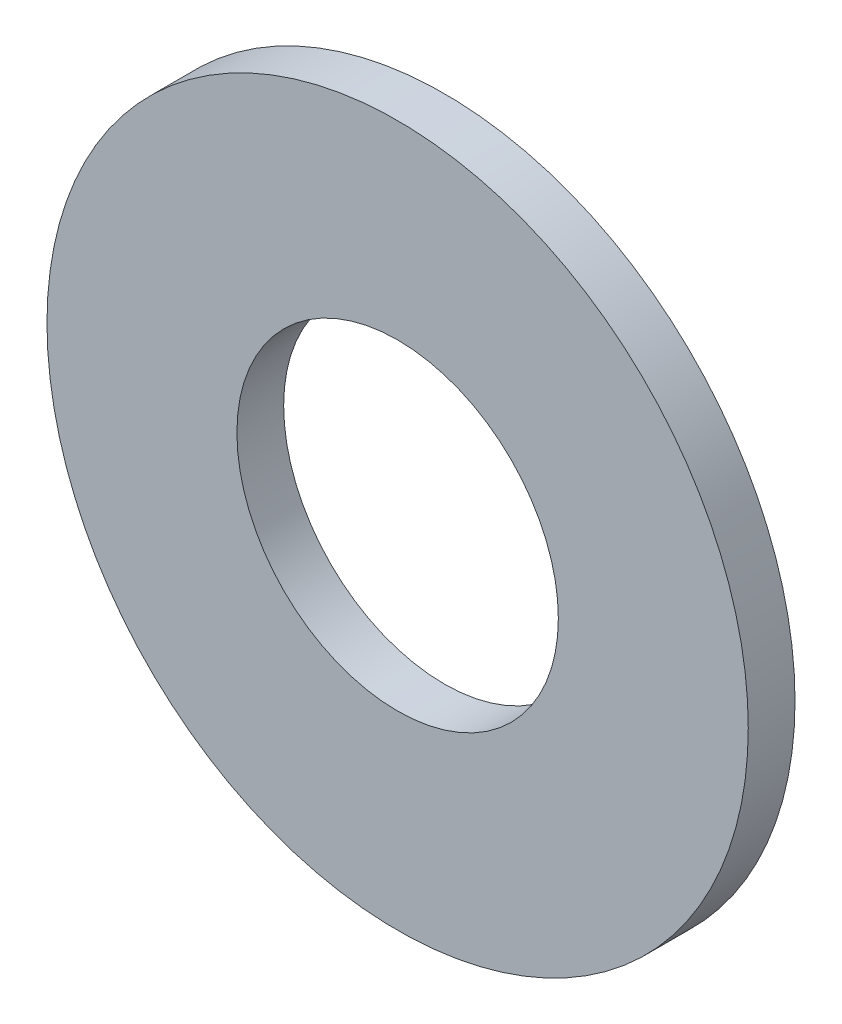
SolidWorks part; units mm, degrees
ref_plane "Front Plane" through (0, 0, 0) normal (0, 0, 1) x (1, 0, 0)
ref_plane "Top Plane" through (0, 0, 0) normal (0, 1, 0) x (1, 0, 0)
ref_plane "Right Plane" through (0, 0, 0) normal (1, 0, 0) x (0, 0, -1)
sketch "Sketch1" plane through (0, 0, 0) normal (0, 0, 1) x (1, 0, 0)
  circle A0 centre (0, 0) radius 6 construction
  circle A1 centre (0, 0) radius 2.75 construction
  point P5 (-2.75, 0)
  point P6 (2.75, 0)
  point P7 (6, 0)
  point P8 (-6, 0)
  point P9 (0, 0)
  point P10 (0, -2.75)
  dimension "OD" = 12
  dimension "ID" = 5.5
sketch "Sketch2" plane through (0, 0, 0) normal (1, 0, 0) x (0, 0, -1)
  line L0 (0, 6) -> (0, -6) construction
  line L1 (0, 6) -> (0, -6) construction
  line L2 (-0.4, 6) -> (0.4, 6) construction
  line L3 (-0.4, 0) -> (0.4, 0) construction
  line L4 (-0.4, -6) -> (0.4, -6) construction
  line L5 (0.4, -6) -> (0.4, 6) construction
  line L6 (-0.4, -6) -> (-0.4, 6) construction
  point P5 (0, 6)
  point P8 (0, 0)
  point P11 (0, -6)
  point P12 (0.4, 6)
  point P13 (0.4, 0)
  point P14 (0.4, -6)
  point P15 (-0.4, -6)
  point P16 (-0.4, 0)
  point P17 (-0.4, 6)
  dimension "Thickness Range" = 0.8
sketch "Sketch3" plane through (0, 0, 0) normal (0, 0, 1) x (1, 0, 0)
  circle A0 centre (0, 0) radius 6 construction
  circle A1 centre (0, 0) radius 2.75 construction
  circle A2 centre (0, 0) radius 6
  circle A3 centre (0, 0) radius 2.75
extrude "Boss-Extrude1" add sketch "Sketch3" along normal mid plane 0.8
equation "\"D1@Boss-Extrude1\" = \"Thickness Range@Sketch2\""
